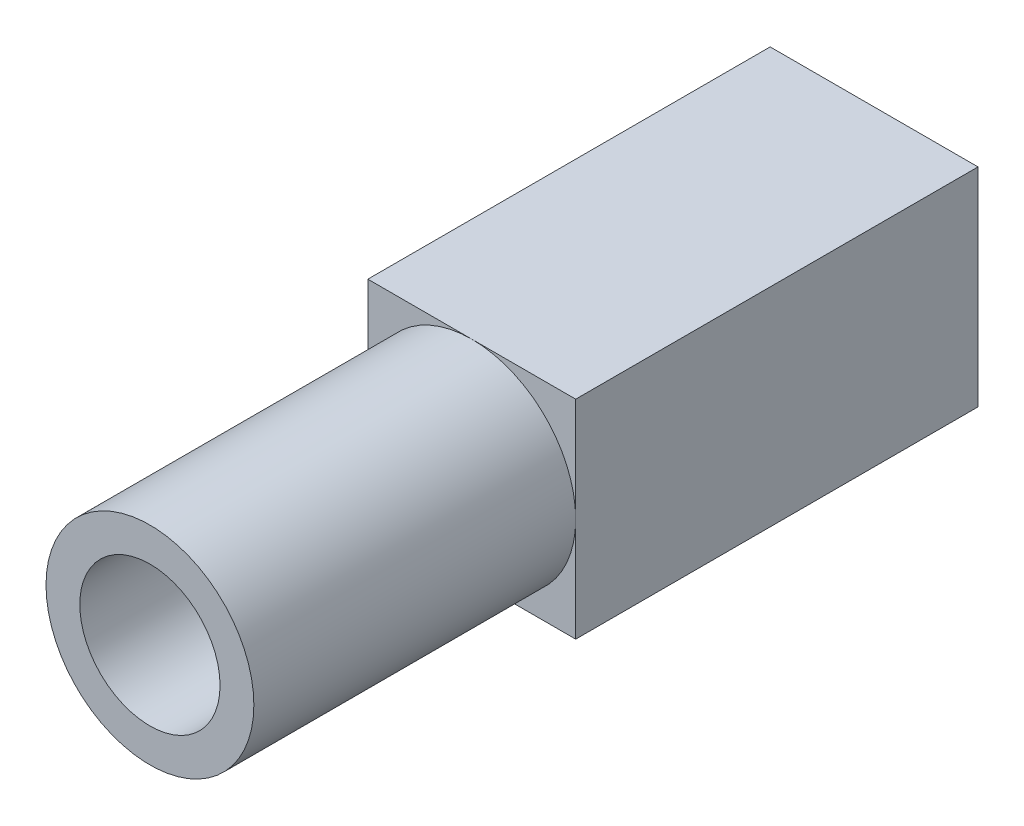
SolidWorks part; units mm, degrees
ref_plane "Front Plane" through (0, 0, 0) normal (0, 0, 1) x (1, 0, 0)
ref_plane "Top Plane" through (0, 0, 0) normal (0, 1, 0) x (1, 0, 0)
ref_plane "Right Plane" through (0, 0, 0) normal (1, 0, 0) x (0, 0, -1)
sketch "Sketch1" plane through (0, 0, 0) normal (0, 0, 1) x (1, 0, 0)
  circle A0 centre (0, 0) radius 3.875
  circle A1 centre (0, 0) radius 2.615
  dimension "D1" = 1.26
  dimension "D2" = 5.23
extrude "Boss-Extrude1" add sketch "Sketch1" along normal blind 22
ref_plane "Plane1" through (0, 0, 10) normal (0, 0, 1) x (1, 0, 0)
sketch "Sketch2" plane through (0, 0, 10) normal (0, 0, 1) x (1, 0, 0)
  line L1 (-3.875, 3.875) -> (3.875, 3.875)
  line L2 (-3.875, 3.875) -> (-3.875, -3.875)
  line L3 (-3.875, -3.875) -> (3.875, -3.875)
  line L4 (3.875, 3.875) -> (3.875, -3.875)
  line L5 (-3.875, 3.875) -> (3.875, -3.875) construction
  line L6 (-3.875, -3.875) -> (3.875, 3.875) construction
  circle A0 centre (0, 0) radius 3.875
  circle A1 centre (0, 0) radius 3.875 construction
  point P0 (0, 0)
extrude "Boss-Extrude2" add sketch "Sketch2" against normal up to surface (10 mm away) contours A0 L1 L2 | A0 L2 L3 | A0 L4 L1 | A0 L3 L4 up to face at (3.875, 0, 0)
sketch "Sketch4" plane through (0, 0, 0) normal (0, 0, -1) x (-1, 0, 0)
  line L4 (-3.875, 3.875) -> (-3.875, -3.875)
  line L5 (-3.875, 3.875) -> (-3.875, -3.875)
  line L6 (-3.875, -3.875) -> (3.875, -3.875)
  line L7 (-3.875, -3.875) -> (3.875, -3.875)
  line L12 (3.875, -3.875) -> (3.875, 3.875)
  line L14 (3.875, -3.875) -> (3.875, 3.875)
  line L16 (3.875, 3.875) -> (-3.875, 3.875)
  line L18 (3.875, 3.875) -> (-3.875, 3.875)
  dimension "D1" = 0
extrude "Boss-Extrude3" add sketch "Sketch4" along normal blind 5
